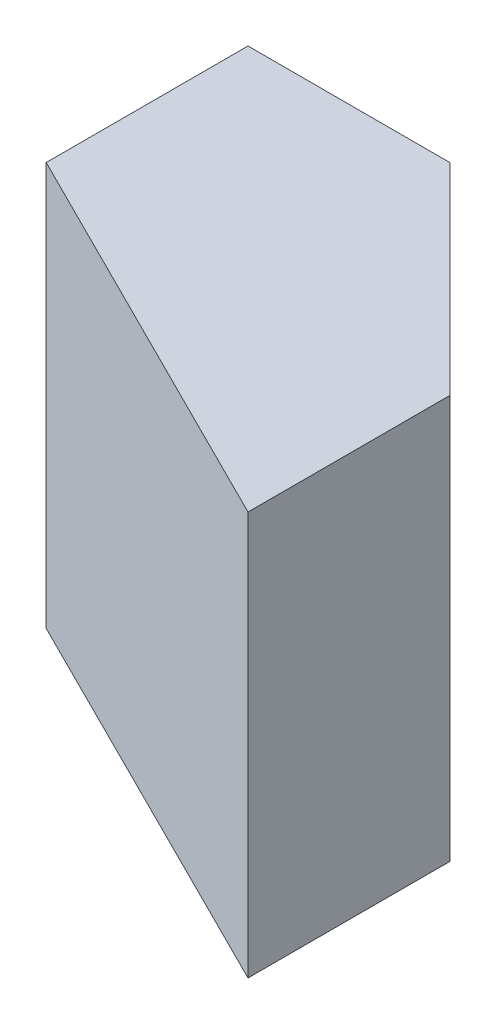
SolidWorks part; units mm, degrees
ref_plane "Front Plane" through (0, 0, 0) normal (0, 0, 1) x (1, 0, 0)
ref_plane "Top Plane" through (0, 0, 0) normal (0, 1, 0) x (1, 0, 0)
ref_plane "Right Plane" through (0, 0, 0) normal (1, 0, 0) x (0, 0, -1)
sketch "Sketch1" plane through (0, 0, 0) normal (0, 0, 1) x (1, 0, 0)
  line L1 (0, 0) -> (20, 0)
  line L2 (0, 0) -> (0, 20)
  line L3 (0, 20) -> (20, 20)
  line L4 (20, 0) -> (20, 20)
  dimension "D1" = 20
  dimension "D2" = 20
extrude "Boss-Extrude1" add sketch "Sketch1" along normal blind 20
sketch "Sketch2" plane through (0, 20, 0) normal (0, 1, 0) x (1, 0, 0)
  line L0 (20, 0) -> (10, 0)
  line L1 (20, 0) -> (0, 0) construction
  line L2 (10, 0) -> (20, -10)
  line L3 (20, -20) -> (20, 0) construction
  line L4 (20, -10) -> (20, 0)
extrude "Cut-Extrude1" cut sketch "Sketch2" against normal blind 20
sketch "Sketch3" plane through (0, 20, 0) normal (0, 1, 0) x (1, 0, 0)
  line L0 (20, -20) -> (0, -20)
  line L1 (0, -20) -> (0, -10)
  line L2 (0, -20) -> (0, 0) construction
  line L3 (0, -10) -> (20, -20)
extrude "Cut-Extrude2" cut sketch "Sketch3" against normal blind 20
